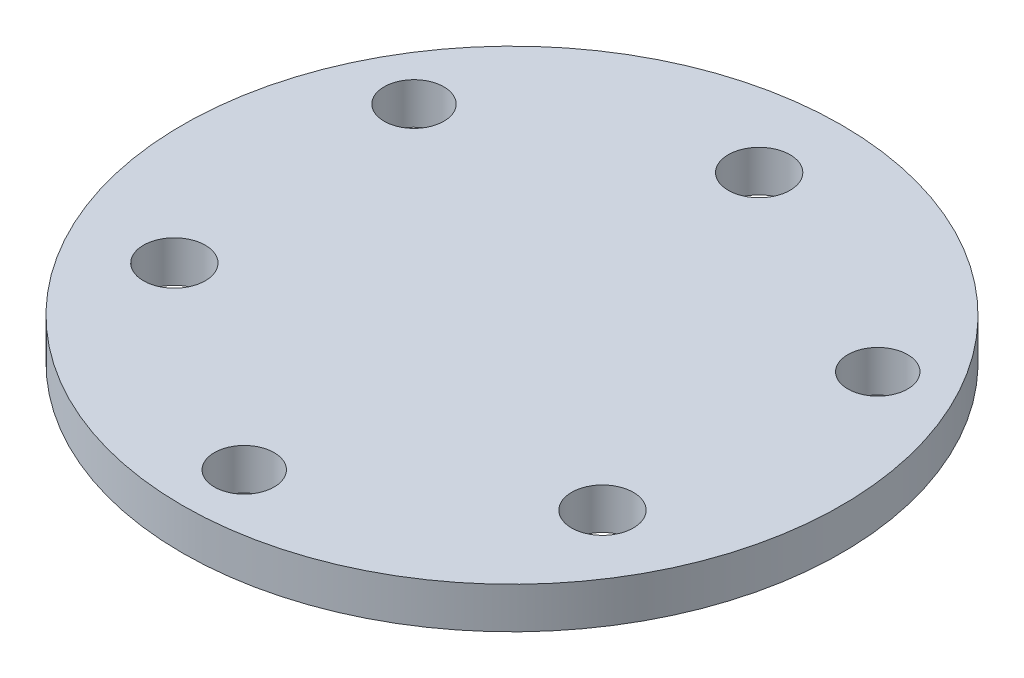
SolidWorks part; units mm, degrees
ref_plane "前视基准面" through (0, 0, 0) normal (0, 0, 1) x (1, 0, 0)
ref_plane "上视基准面" through (0, 0, 0) normal (0, 1, 0) x (1, 0, 0)
ref_plane "右视基准面" through (0, 0, 0) normal (1, 0, 0) x (0, 0, -1)
sketch "草图1" plane through (0, 0, 0) normal (0, 1, 0) x (1, 0, 0)
  line L1 (0, 12) -> (-10.3923, -6) construction
  line L2 (-10.3923, -6) -> (10.3923, -6) construction
  line L3 (10.3923, -6) -> (0, 12) construction
  line L4 (0, -13) -> (11.2583, 6.5) construction
  line L5 (11.2583, 6.5) -> (-11.2583, 6.5) construction
  line L6 (-11.2583, 6.5) -> (0, -13) construction
  circle A0 centre (0, 0) radius 16
  circle A1 centre (0, 0) radius 13 construction
  circle A2 centre (0, 0) radius 12 construction
  circle A3 centre (0, 0) radius 6 construction
  circle A4 centre (0, 0) radius 6.5 construction
  circle A5 centre (-10.3923, -6) radius 1.5
  circle A6 centre (0, 12) radius 1.5
  circle A7 centre (10.3923, -6) radius 1.5
  circle A8 centre (-11.2583, 6.5) radius 1.45
  circle A9 centre (0, -13) radius 1.45
  circle A10 centre (11.2583, 6.5) radius 1.45
  dimension "D1" = 32
  dimension "D2" = 24
  dimension "D3" = 26
  dimension "D4" = 3
  dimension "D5" = 2.9
extrude "凸台-拉伸1" add sketch "草图1" along normal blind 2
